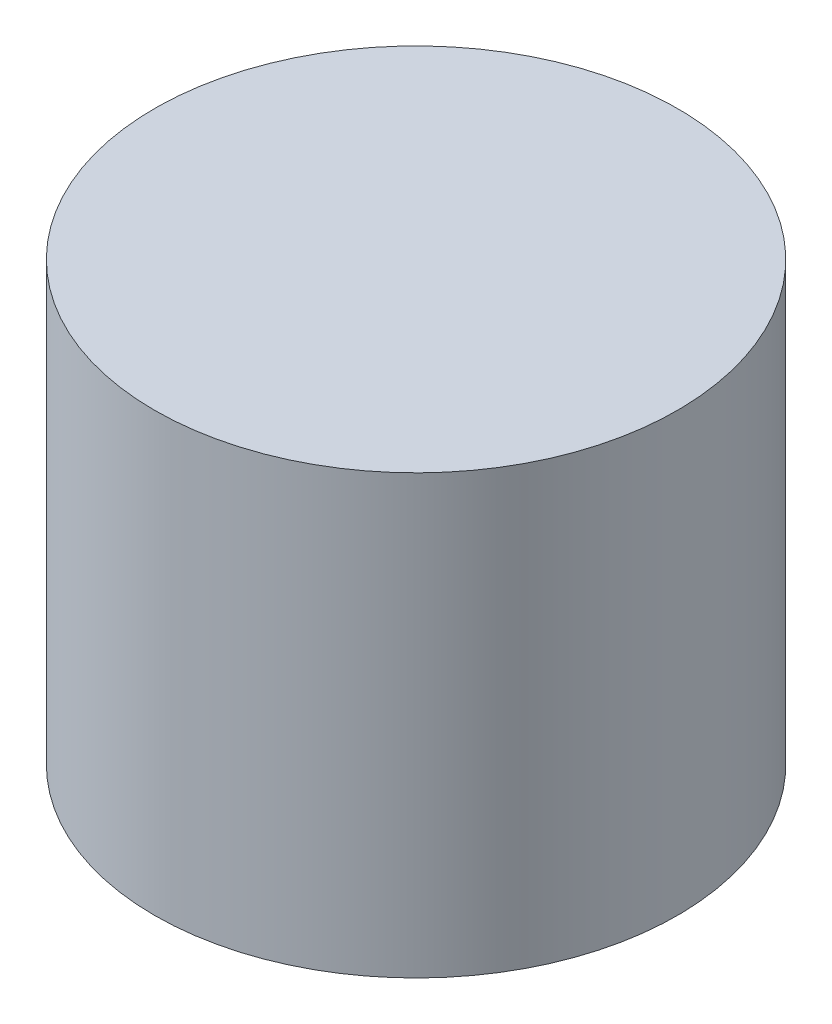
SolidWorks part; units mm, degrees
ref_plane "Front Plane" through (0, 0, 0) normal (0, 0, 1) x (1, 0, 0)
ref_plane "Top Plane" through (0, 0, 0) normal (0, 1, 0) x (1, 0, 0)
ref_plane "Right Plane" through (0, 0, 0) normal (1, 0, 0) x (0, 0, -1)
sketch "Sketch1" plane through (0, 0, 0) normal (0, 1, 0) x (1, 0, 0)
  circle A0 centre (0, 0) radius 3.49
  dimension "D1" = 6.98
extrude "Boss-Extrude1" add sketch "Sketch1" along normal mid plane 5.84
